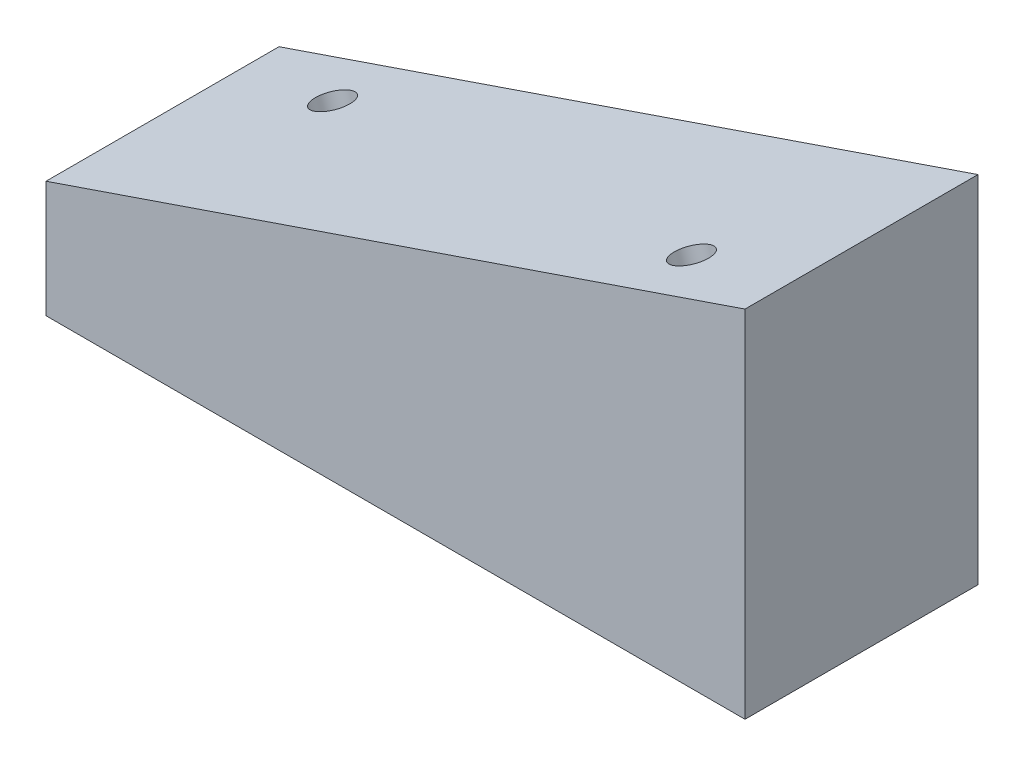
SolidWorks part; units mm, degrees
material "6061-T6 (SS)"
ref_plane "Front Plane" through (0, 0, 0) normal (0, 0, 1) x (1, 0, 0)
ref_plane "Top Plane" through (0, 0, 0) normal (0, 1, 0) x (1, 0, 0)
ref_plane "Right Plane" through (0, 0, 0) normal (1, 0, 0) x (0, 0, -1)
sketch "Sketch1" plane through (0, 0, 0) normal (0, 0, 1) x (1, 0, 0)
  line L0 (-76.2, 0) -> (76.2, 0)
  line L1 (76.2, 0) -> (76.2, 77.4593)
  line L2 (76.2, 77.4593) -> (-76.2, 25.4)
  line L3 (-76.2, 25.4) -> (-76.2, 0)
  point P3 (0, 0)
  dimension "D1" = 152.4
  dimension "D2" = 18.86
  dimension "D3" = 25.4
extrude "Boss-Extrude1" add sketch "Sketch1" against normal blind 50.8
hole_wizard "3/8-16 Tapped Hole1" positions "Sketch4" profile "Sketch3" tap size "3/8-16" standard "ANSI Inch"
sketch "Sketch4" plane through (-15.7324, 46.0555, 0) normal (-0.3233, 0.9463, 0) x (0.9463, 0.3233, 0)
  line L0 (-38.1438, 38.1) -> (71.3937, 12.7) construction
  line L2 (-63.8982, 50.8) -> (-63.8982, 0) construction
  line L3 (97.1482, 0) -> (-63.8982, 0) construction
  point P0 (-38.1438, 38.1)
  point P2 (71.3937, 12.7)
  point P10 (16.625, 25.4)
  point P14 (-63.8982, 25.4)
  point P22 (16.625, 0)
  dimension "D1" = 25.4
  dimension "D2" = 109.5375
cosmetic thread "Hole Thread1" parameters "D1"=19.05, "D2"=9.525
cosmetic thread "Hole Thread2" parameters "D1"=19.05, "D2"=9.525
sketch "Sketch3" plane through (-51.8283, 33.7253, -38.1) normal (0, 0, 1) x (-0.9463, -0.3233, 0)
  line L0 (0, 0) -> (0, 27.7847)
  line L1 (0, 27.7847) -> (3.9687, 25.4)
  line L2 (3.9687, 25.4) -> (3.9687, 0)
  line L5 (3.9687, 0) -> (0, 0)
  line L10 (0, 27.7847) -> (-3.9688, 25.4) construction
  line L11 (0, -6.35) -> (0, 107.95) construction
  dimension "Tap Drill Dia." = 7.9375
  dimension "Tap Drill Depth" = 25.4
  dimension "Drill Angle" = 118
hole_wizard "3/8-16 Tapped Hole2" positions "Sketch6" profile "Sketch5" tap size "3/8-16" standard "ANSI Inch"
sketch "Sketch6" plane through (0, 0, 0) normal (0, -1, 0) x (-1, 0, 0)
  line L0 (76.2, 50.8) -> (76.2, 0) construction
  line L1 (38.1, 25.4) -> (-38.1, 25.4) construction
  line L3 (76.2, 50.8) -> (-76.2, 50.8) construction
  point P0 (38.1, 25.4)
  point P2 (-38.1, 25.4)
  point P7 (76.2, 25.4)
  point P20 (0, 25.4)
  point P23 (0, 50.8)
  dimension "D1" = 76.2
cosmetic thread "Hole Thread3"
cosmetic thread "Hole Thread4"
sketch "Sketch5" plane through (-38.1, 0, -25.4) normal (1, 0, 0) x (0, 0, -1)
  line L0 (0, 0) -> (0, 27.7847)
  line L1 (0, 27.7847) -> (3.9687, 25.4)
  line L2 (3.9687, 25.4) -> (3.9687, 0)
  line L5 (3.9687, 0) -> (0, 0)
  line L10 (0, 27.7847) -> (-3.9688, 25.4) construction
  line L11 (0, -6.35) -> (0, 107.95) construction
  dimension "Tap Drill Dia." = 7.9375
  dimension "Tap Drill Depth" = 25.4
  dimension "Drill Angle" = 118
